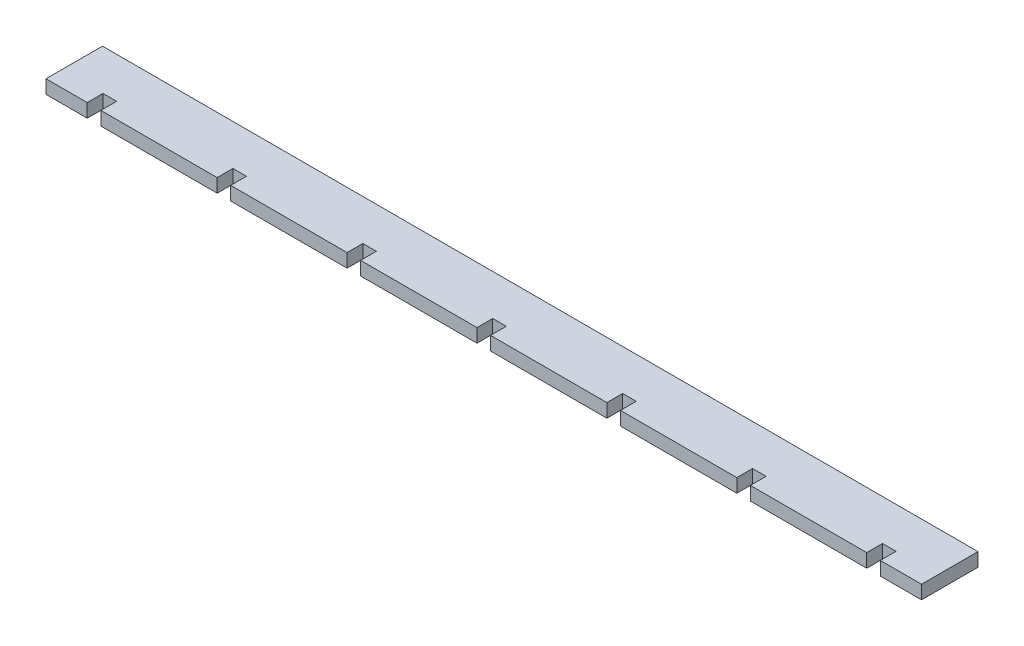
SolidWorks part; units mm, degrees
ref_plane "Front Plane" through (0, 0, 0) normal (0, 0, 1) x (1, 0, 0)
ref_plane "Top Plane" through (0, 0, 0) normal (0, 1, 0) x (1, 0, 0)
ref_plane "Right Plane" through (0, 0, 0) normal (1, 0, 0) x (0, 0, -1)
sketch "Sketch1" plane through (0, 0, 0) normal (0, 1, 0) x (1, 0, 0)
  line L1 (-98.425, 0) -> (98.425, 0)
  line L2 (-98.425, 0) -> (-98.425, 12.7)
  line L3 (-98.425, 12.7) -> (98.425, 12.7)
  line L4 (98.425, 0) -> (98.425, 12.7)
  point P4 (0, 0)
  dimension "D1" = 12.7
  dimension "D2" = 196.85
extrude "Boss-Extrude1" add sketch "Sketch1" along normal blind 3.048
sketch "Sketch2" plane through (0, 3.048, 0) normal (0, 1, 0) x (1, 0, 0)
  line L0 (89.154, 0) -> (89.154, 3.5412)
  line L1 (-98.425, 0) -> (98.425, 0) construction
  line L2 (89.154, 3.5412) -> (86.106, 3.5412)
  line L3 (86.106, 3.5412) -> (86.106, 0)
  line L4 (86.106, 0) -> (89.154, 0)
  line L5 (89.154, 7.1474) -> (89.154, -23.2346) construction
  line L6 (59.944, 7.1474) -> (59.944, -23.2346) construction
  line L7 (56.896, 3.5412) -> (59.944, 3.5412)
  line L8 (56.896, 3.5412) -> (56.896, 0)
  line L9 (56.896, 0) -> (59.944, 0)
  line L10 (59.944, 3.5412) -> (59.944, 0)
  line L11 (27.686, 3.5412) -> (30.734, 3.5412)
  line L12 (27.686, 3.5412) -> (27.686, 0)
  line L13 (27.686, 0) -> (30.734, 0)
  line L14 (30.734, 3.5412) -> (30.734, 0)
  line L15 (-1.524, 3.5412) -> (1.524, 3.5412)
  line L16 (-1.524, 3.5412) -> (-1.524, 0)
  line L17 (-1.524, 0) -> (1.524, 0)
  line L18 (1.524, 3.5412) -> (1.524, 0)
  line L19 (-30.734, 3.5412) -> (-27.686, 3.5412)
  line L20 (-30.734, 3.5412) -> (-30.734, 0)
  line L21 (-30.734, 0) -> (-27.686, 0)
  line L22 (-27.686, 3.5412) -> (-27.686, 0)
  line L23 (-59.944, 3.5412) -> (-56.896, 3.5412)
  line L24 (-59.944, 3.5412) -> (-59.944, 0)
  line L25 (-59.944, 0) -> (-56.896, 0)
  line L26 (-56.896, 3.5412) -> (-56.896, 0)
  line L27 (-89.154, 3.5412) -> (-86.106, 3.5412)
  line L28 (-89.154, 3.5412) -> (-89.154, 0)
  line L29 (-89.154, 0) -> (-86.106, 0)
  line L30 (-86.106, 3.5412) -> (-86.106, 0)
  line L31 (30.734, 7.1474) -> (30.734, -23.2346) construction
  line L32 (1.524, 7.1474) -> (1.524, -23.2346) construction
  line L33 (-27.686, 7.1474) -> (-27.686, -23.2346) construction
  line L34 (-56.896, 7.1474) -> (-56.896, -23.2346) construction
  line L35 (-86.106, 7.1474) -> (-86.106, -23.2346) construction
extrude "Cut-Extrude1" cut sketch "Sketch2" against normal through all
